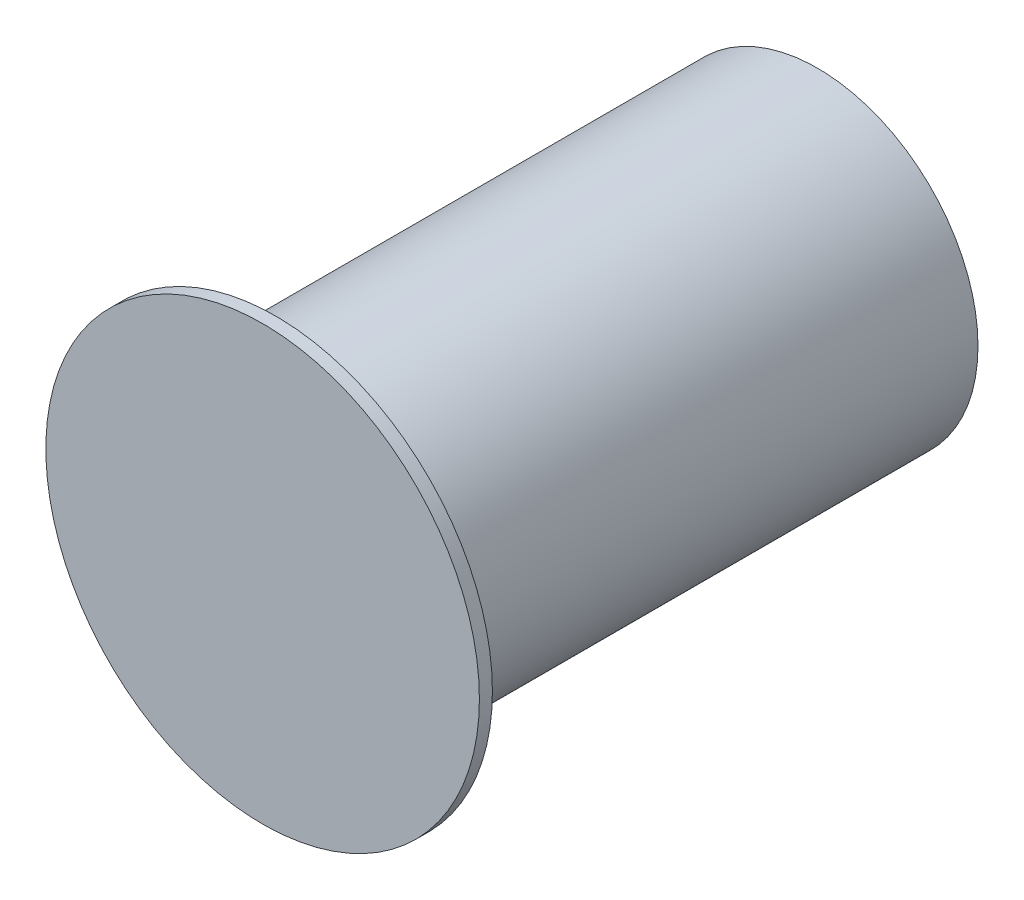
SolidWorks part; units mm, degrees
ref_plane "Front Plane" through (0, 0, 0) normal (0, 0, 1) x (1, 0, 0)
ref_plane "Top Plane" through (0, 0, 0) normal (0, 1, 0) x (1, 0, 0)
ref_plane "Right Plane" through (0, 0, 0) normal (1, 0, 0) x (0, 0, -1)
sketch "Sketch2" plane through (0, 0, 0) normal (0, 0, 1) x (1, 0, 0)
  circle A0 centre (0, 0) radius 10
  dimension "D1" = 20
extrude "Boss-Extrude1" add sketch "Sketch2" along normal blind 0.6
sketch "Sketch3" plane through (0, 0, 0) normal (0, 0, -1) x (-1, 0, 0)
  circle A0 centre (0, 0) radius 7.4
  dimension "D1" = 14.8
extrude "Boss-Extrude2" add sketch "Sketch3" along normal blind 25
sketch "Sketch4" plane through (0, 0, -25) normal (0, 0, -1) x (-1, 0, 0)
  circle A0 centre (0, 0) radius 5
  dimension "D1" = 10
extrude "Cut-Extrude1" cut sketch "Sketch4" against normal blind 2
sketch "Sketch5" plane through (0, 0, -23) normal (0, 0, -1) x (-1, 0, 0)
  circle A0 centre (0, 0) radius 3
  dimension "D1" = 6
extrude "Cut-Extrude2" cut sketch "Sketch5" against normal blind 2.5
sketch "Sketch6" plane through (0, 0, -20.5) normal (0, 0, -1) x (-1, 0, 0)
  line L0 (0, 0) -> (0, -3) construction
  line L1 (-2, 2.2361) -> (-2, -2.2361)
  line L2 (2, 2.2361) -> (2, -2.2361)
  circle A0 centre (0, 0) radius 3 construction
  circle A2 centre (0, 0) radius 3 construction
  arc A3 (-2, -2.2361) -> (2, -2.2361) centre (0, 0) ccw
  arc A4 (2, 2.2361) -> (-2, 2.2361) centre (0, 0) ccw
  dimension "D1" = 2
extrude "Cut-Extrude3" cut sketch "Sketch6" against normal blind 7
